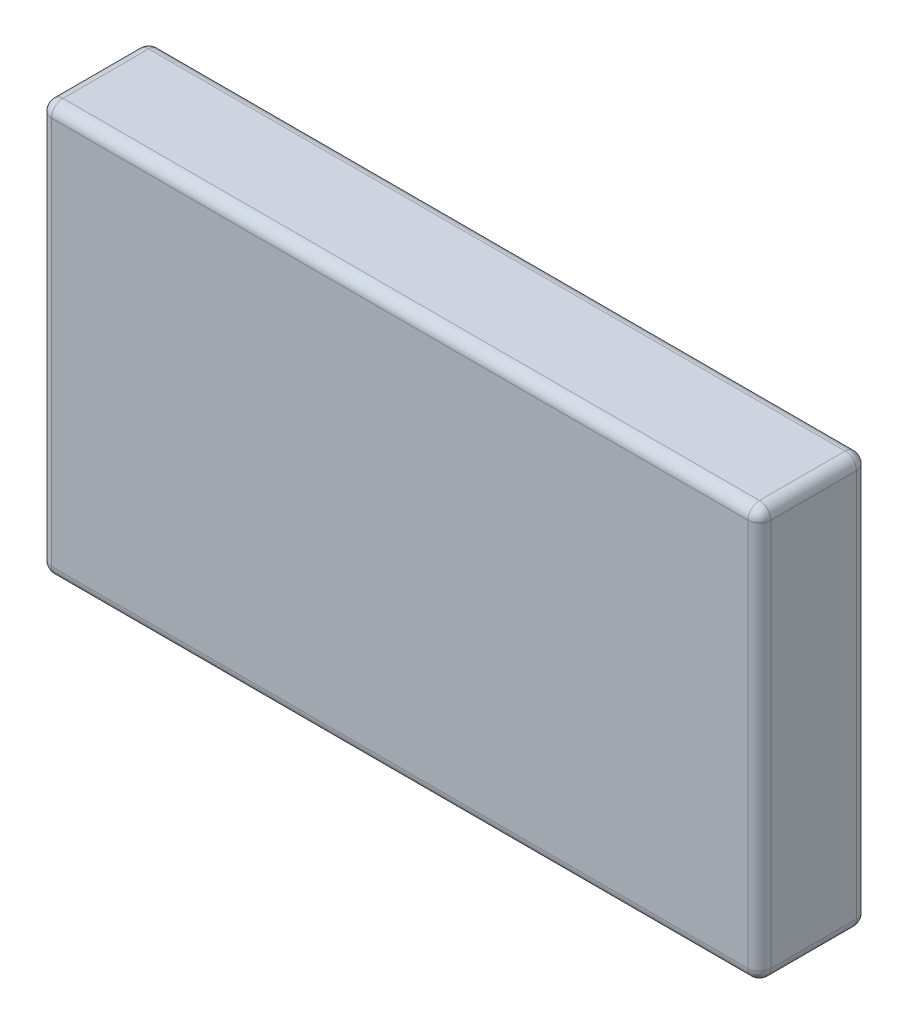
SolidWorks part; units mm, degrees
ref_plane "前视基准面" through (0, 0, 0) normal (0, 0, 1) x (1, 0, 0)
ref_plane "上视基准面" through (0, 0, 0) normal (0, 1, 0) x (1, 0, 0)
ref_plane "右视基准面" through (0, 0, 0) normal (1, 0, 0) x (0, 0, -1)
sketch "草图1" plane through (0, 0, 0) normal (0, 0, 1) x (1, 0, 0)
  line L1 (-63, 36) -> (63, 36)
  line L2 (-63, 36) -> (-63, -36)
  line L3 (-63, -36) -> (63, -36)
  line L4 (63, 36) -> (63, -36)
  point P4 (-63, 0)
  dimension "D1" = 126
  dimension "D2" = 72
  dimension "D3" = 63
  dimension "D4" = 36
extrude "凸台-拉伸1" add sketch "草图1" along normal blind 19
fillet "圆角1" radius 2 12 edges at (-63, 0, 0) (0, -36, 0) (63, 0, 0) (0, 36, 0) (-63, 0, 19) (0, -36, 19) (0, 36, 19) (-63, 36, 9.5) (63, 36, 9.5) (63, -36, 9.5) (-63, -36, 9.5) (63, 0, 19)
